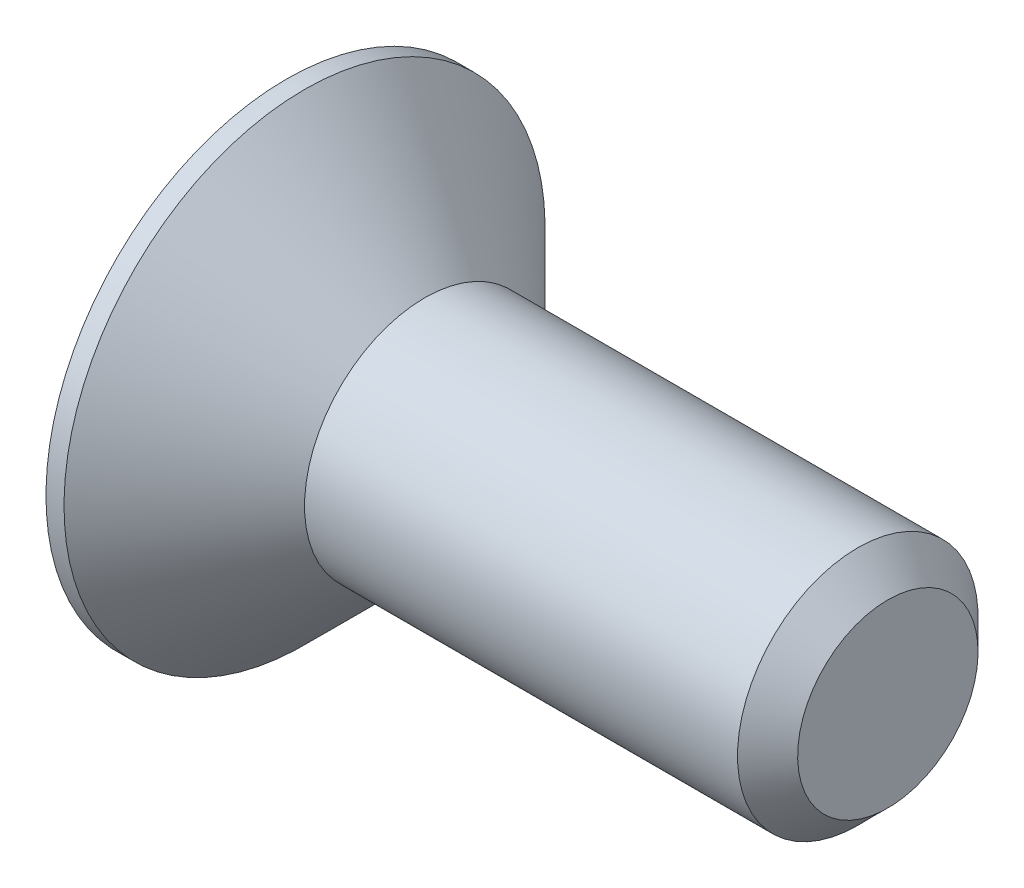
SolidWorks part; units mm, degrees
ref_plane "Plan de face" through (0, 0, 0) normal (0, 0, 1) x (1, 0, 0)
ref_plane "Plan de dessus" through (0, 0, 0) normal (0, 1, 0) x (1, 0, 0)
ref_plane "Plan de droite" through (0, 0, 0) normal (1, 0, 0) x (0, 0, -1)
sketch "Esquisse1" plane through (0, 0, 0) normal (0, 0, 1) x (1, 0, 0)
  line L0 (0, 0) -> (0, 4)
  line L1 (0, 4) -> (0.3, 4)
  line L2 (0.3, 4) -> (2.3, 2)
  line L3 (2.3, 2) -> (10, 2)
  line L4 (10, 2) -> (10, 0)
  line L5 (10, 0) -> (0, 0) construction
  line L6 (0, 0) -> (10, 0)
  dimension "D1" = 2.3
  dimension "D2" = 10
  dimension "D3" = 4
  dimension "D4" = 8
  dimension "D5" = 45
revolve "Révolution1" add sketch "Esquisse1" angle 360 about L5
chamfer "Chanfrein1" distance 0.5 angle 45 1 edges at (10, 2, 0)
sketch "Esquisse2" plane through (0, 0, 0) normal (-1, 0, 0) x (0, 0, 1)
  line L1 (0, 1.4434) -> (-1.25, 0.7217)
  line L2 (-1.25, 0.7217) -> (-1.25, -0.7217)
  line L3 (-1.25, -0.7217) -> (0, -1.4434)
  line L4 (0, -1.4434) -> (1.25, -0.7217)
  line L5 (1.25, -0.7217) -> (1.25, 0.7217)
  line L6 (1.25, 0.7217) -> (0, 1.4434)
  circle A0 centre (0, 0) radius 1.25 construction
  dimension "D1" = 2.5
extrude "Enlèv. mat.-Extru.1" cut sketch "Esquisse2" against normal blind 1.8
